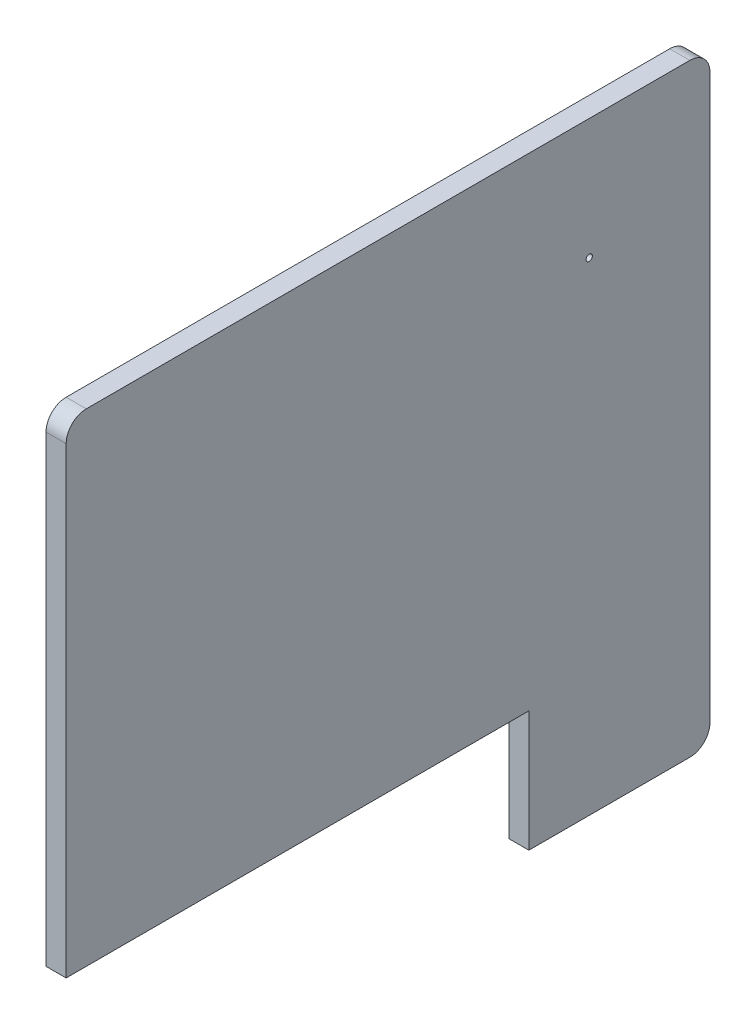
SolidWorks part; units mm, degrees
ref_plane "Front Plane" through (0, 0, 0) normal (0, 0, 1) x (1, 0, 0)
ref_plane "Top Plane" through (0, 0, 0) normal (0, 1, 0) x (1, 0, 0)
ref_plane "Right Plane" through (0, 0, 0) normal (1, 0, 0) x (0, 0, -1)
sketch "Sketch1" plane through (0, 0, 0) normal (1, 0, 0) x (0, 0, -1)
  line L0 (82.55, 0) -> (82.55, 76.2) construction
  line L1 (0, 0) -> (101.6, 0)
  line L2 (0, 0) -> (0, 95.25)
  line L3 (0, 95.25) -> (101.6, 95.25)
  line L4 (101.6, 0) -> (101.6, 95.25)
  line L5 (82.55, 76.2) -> (0, 76.2) construction
  circle A0 centre (82.55, 76.2) radius 0.5
  dimension "D5" = 1
  dimension "D1" = 101.6
  dimension "D2" = 95.25
  dimension "D3" = 76.2
  dimension "D4" = 82.55
extrude "Boss-Extrude1" add sketch "Sketch1" along normal blind 3.175
sketch "Sketch2" plane through (3.175, 0, 0) normal (1, 0, 0) x (0, 0, -1)
  line L1 (0, 0) -> (73.025, 0)
  line L2 (0, 0) -> (0, 19.05)
  line L3 (0, 19.05) -> (73.025, 19.05)
  line L4 (73.025, 0) -> (73.025, 19.05)
  dimension "D1" = 73.025
  dimension "D2" = 19.05
extrude "Cut-Extrude1" cut sketch "Sketch2" against normal through all
fillet "Fillet1" radius 3.175 3 edges at (1.5875, 0, -101.6) (1.5875, 95.25, -101.6) (1.5875, 95.25, 0)
